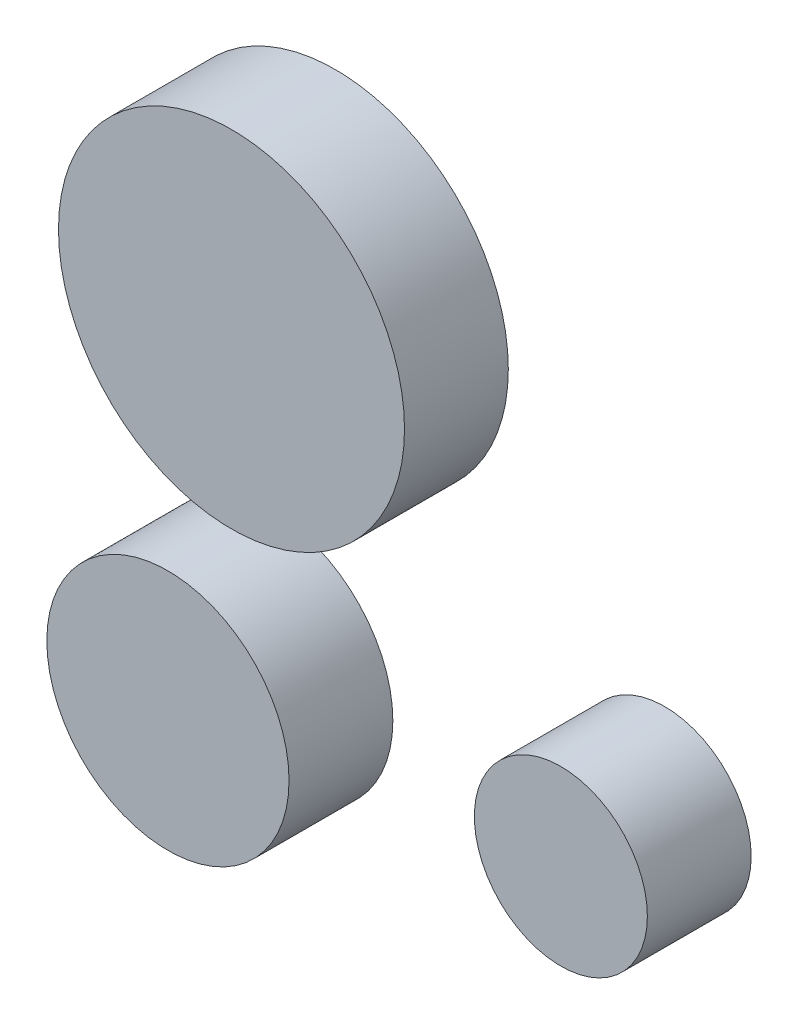
SolidWorks part; units mm, degrees
material "Polyurethane Foam Flexible"
ref_plane "Front Plane" through (0, 0, 0) normal (0, 0, 1) x (1, 0, 0)
ref_plane "Top Plane" through (0, 0, 0) normal (0, 1, 0) x (1, 0, 0)
ref_plane "Right Plane" through (0, 0, 0) normal (1, 0, 0) x (0, 0, -1)
sketch "Sketch1" plane through (0, 0, 0) normal (0, 0, 1) x (1, 0, 0)
  circle A0 centre (0, 0) radius 12.7
  circle A1 centre (24.1763, -22.0556) radius 6.35
  circle A2 centre (-4.6656, -26.5798) radius 8.89
  point P5 (24.1763, -22.0556)
  point P8 (-4.6656, -26.5798)
  dimension "D1" = 25.4
  dimension "D2" = 17.78
  dimension "D3" = 12.7
extrude "Boss-Extrude1" add sketch "Sketch1" along normal blind 7.62
